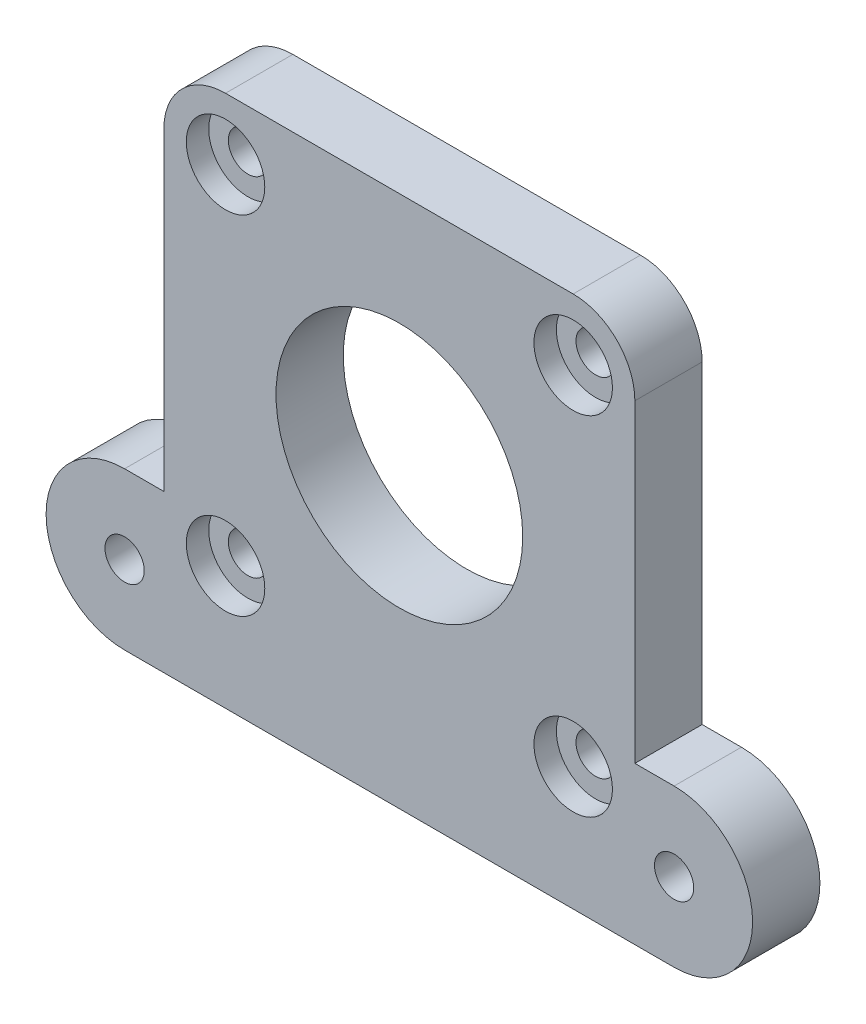
SolidWorks part; units mm, degrees
ref_plane "Plano frontal" through (0, 0, 0) normal (0, 0, 1) x (1, 0, 0)
ref_plane "Plano superior" through (0, 0, 0) normal (0, 1, 0) x (1, 0, 0)
ref_plane "Plano direito" through (0, 0, 0) normal (1, 0, 0) x (0, 0, -1)
sketch "Esboço1" plane through (0, 0, 0) normal (0, 0, 1) x (1, 0, 0)
  line L0 (0, 0) -> (0, -38.2551) construction
  line L1 (-21, 23.75) -> (21, 23.75)
  line L2 (-21, 23.75) -> (-21, -9.75)
  line L3 (-21, -23.75) -> (21, -23.75)
  line L4 (21, 23.75) -> (21, -9.75)
  line L5 (-21, 23.75) -> (21, -23.75) construction
  line L6 (-21, -23.75) -> (21, 23.75) construction
  line L7 (0, 42.2449) -> (0, 2.75) construction
  line L8 (0, 2.75) -> (12.8208, 2.75) construction
  line L9 (15.5, 23.75) -> (15.5, 18.25) construction
  line L10 (15.5, 18.25) -> (21, 18.25) construction
  line L11 (21, -23.75) -> (24.5, -23.75)
  line L12 (24.5, -9.75) -> (21, -9.75)
  line L14 (-21, -23.75) -> (-24.5, -23.75)
  line L15 (-24.5, -9.75) -> (-21, -9.75)
  circle A0 centre (24.5, -16.75) radius 1.75
  circle A1 centre (0, 2.75) radius 11
  circle A2 centre (15.5, 18.25) radius 1.75
  circle A3 centre (15.5, -12.75) radius 1.75
  circle A4 centre (-15.5, 18.25) radius 1.75
  circle A5 centre (-15.5, -12.75) radius 1.75
  circle A6 centre (24.5, -16.75) radius 3.5 construction
  circle A7 centre (-24.5, -16.75) radius 1.75
  arc A8 (24.5, -23.75) -> (24.5, -9.75) centre (24.5, -16.75) ccw
  arc A9 (-24.5, -23.75) -> (-24.5, -9.75) centre (-24.5, -16.75) cw
  point P0 (0, 0)
  dimension "D3" = 22
  dimension "D5" = 3.5
  dimension "D8" = 7
  dimension "D1" = 4
  dimension "D2" = 31
  dimension "D4" = 31
  dimension "D6" = 42
  dimension "D7" = 7
extrude "Ressalto-extrusão1" add sketch "Esboço1" along normal blind 6
fillet "Filete1" radius 5.5 2 edges at (21, 23.75, 3) (-21, 23.75, 3)
sketch "Esboço2" plane through (0, 0, 6) normal (0, 0, 1) x (1, 0, 0)
  circle A4 centre (-15.5, 18.25) radius 3.5
  circle A5 centre (15.5, 18.25) radius 3.5
  circle A6 centre (15.5, -12.75) radius 3.5
  circle A7 centre (-15.5, -12.75) radius 3.5
  dimension "D1" = 7
extrude "Corte-extrusão1" cut sketch "Esboço2" against normal blind 2
